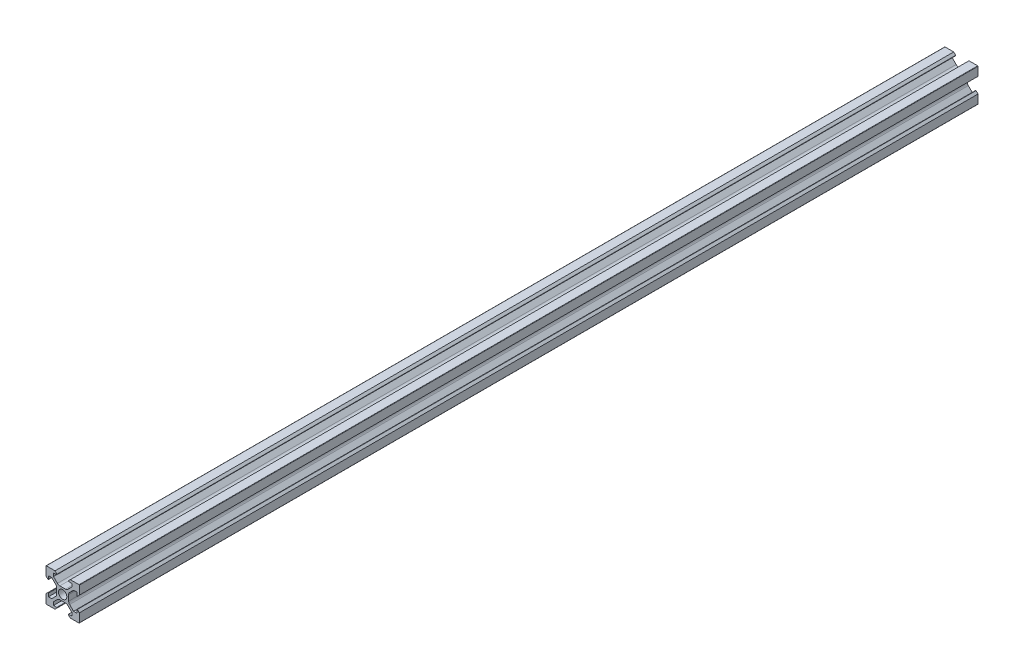
SolidWorks part; units mm, degrees
material "Liga 1350"
ref_plane "Plano frontal" through (0, 0, 0) normal (0, 0, 1) x (1, 0, 0)
ref_plane "Plano superior" through (0, 0, 0) normal (0, 1, 0) x (1, 0, 0)
ref_plane "Plano direito" through (0, 0, 0) normal (1, 0, 0) x (0, 0, -1)
sketch "Esboço1" plane through (0, 0, 0) normal (0, 0, 1) x (1, 0, 0)
  line L0 (0, 13.8681) -> (0, -15.879) construction
  line L1 (-4.6, -10) -> (-9.8, -10)
  line L2 (-3.4414, -8.8414) -> (-4.6, -10)
  line L3 (-4.1858, -3.1251) -> (-6.5607, -5.5)
  line L4 (-10, 9.8) -> (-10, 4.6)
  line L5 (-5.5, -8.5) -> (-3.5828, -8.5)
  line L6 (-5.5, -8.5) -> (-5.5, -6.5607)
  line L7 (-8.5, -5.5) -> (-8.5, -3.5828)
  line L8 (-21.5514, 0) -> (2.5, 0) construction
  line L9 (-3.1251, 4.1858) -> (-5.5, 6.5607)
  line L10 (-8.8414, -3.4414) -> (-10, -4.6)
  line L11 (-8.5, 5.5) -> (-6.5607, 5.5)
  line L12 (-8.8414, 3.4414) -> (-10, 4.6)
  line L13 (-8.5, -5.5) -> (-6.5607, -5.5)
  line L14 (-8.5, 5.5) -> (-8.5, 3.5828)
  line L15 (-3.1251, -4.1858) -> (-5.5, -6.5607)
  line L16 (-21.5514, 0) -> (20.6623, 0) construction
  line L17 (-8.5, 10) -> (-8.5, -10) construction
  line L18 (-10, -9.8) -> (-10, -4.6)
  line L19 (-21.5514, 5.5) -> (20.6623, 5.5) construction
  line L21 (-10, 10) -> (-10, -10) construction
  line L22 (3.6, 1.7109) -> (3.6, 0) construction
  line L23 (21.5514, 0) -> (-2.5, 0) construction
  line L24 (4.6, 10) -> (9.8, 10)
  line L25 (-5.5, 8.5) -> (-5.5, 6.5607)
  line L26 (3.4414, 8.8414) -> (4.6, 10)
  line L27 (-5.5, 8.5) -> (-3.5828, 8.5)
  line L28 (4.1858, 3.1251) -> (6.5607, 5.5)
  line L29 (5.5, 8.5) -> (3.5828, 8.5)
  line L30 (5.5, 8.5) -> (5.5, 6.5607)
  line L31 (-3.6, 1.7109) -> (-3.6, -1.7109)
  line L33 (10, -9.8) -> (10, -4.6)
  line L34 (-4.1858, 3.1251) -> (-6.5607, 5.5)
  line L35 (-3.4414, 8.8414) -> (-4.6, 10)
  line L36 (-4.6, 10) -> (-9.8, 10)
  line L37 (3.1251, -4.1858) -> (5.5, -6.5607)
  line L38 (8.5, 5.5) -> (8.5, 3.5828)
  line L39 (8.5, -5.5) -> (6.5607, -5.5)
  line L40 (8.8414, 3.4414) -> (10, 4.6)
  line L41 (8.5, 5.5) -> (6.5607, 5.5)
  line L42 (8.8414, -3.4414) -> (10, -4.6)
  line L43 (3.1251, 4.1858) -> (5.5, 6.5607)
  line L44 (8.5, -5.5) -> (8.5, -3.5828)
  line L45 (5.5, -8.5) -> (5.5, -6.5607)
  line L46 (5.5, -8.5) -> (3.5828, -8.5)
  line L47 (10, 9.8) -> (10, 4.6)
  line L48 (4.1858, -3.1251) -> (6.5607, -5.5)
  line L49 (3.4414, -8.8414) -> (4.6, -10)
  line L50 (4.6, -10) -> (9.8, -10)
  line L51 (-1.7109, 3.6) -> (1.7109, 3.6)
  line L52 (3.6, 1.7109) -> (3.6, -1.7109)
  line L53 (1.7109, -3.6) -> (-1.7109, -3.6)
  circle A0 centre (0, 0) radius 2.5
  arc A1 (-3.6, 1.7109) -> (-4.1858, 3.1251) centre (-5.6, 1.7109) ccw
  arc A2 (-8.5, 3.5828) -> (-8.8414, 3.4414) centre (-8.7, 3.5828) cw
  arc A3 (-9.8, 10) -> (-10, 9.8) centre (-9.8, 9.8) ccw
  arc A4 (-1.7109, 3.6) -> (-3.1251, 4.1858) centre (-1.7109, 5.6) cw
  arc A5 (-3.5828, 8.5) -> (-3.4414, 8.8414) centre (-3.5828, 8.7) ccw
  arc A6 (-3.5828, -8.5) -> (-3.4414, -8.8414) centre (-3.5828, -8.7) cw
  arc A7 (-1.7109, -3.6) -> (-3.1251, -4.1858) centre (-1.7109, -5.6) ccw
  arc A8 (-9.8, -10) -> (-10, -9.8) centre (-9.8, -9.8) cw
  arc A9 (-8.5, -3.5828) -> (-8.8414, -3.4414) centre (-8.7, -3.5828) ccw
  arc A10 (-3.6, -1.7109) -> (-4.1858, -3.1251) centre (-5.6, -1.7109) cw
  arc A11 (3.6, -1.7109) -> (4.1858, -3.1251) centre (5.6, -1.7109) ccw
  arc A12 (8.5, -3.5828) -> (8.8414, -3.4414) centre (8.7, -3.5828) cw
  arc A13 (9.8, -10) -> (10, -9.8) centre (9.8, -9.8) ccw
  arc A14 (1.7109, -3.6) -> (3.1251, -4.1858) centre (1.7109, -5.6) cw
  arc A15 (3.5828, -8.5) -> (3.4414, -8.8414) centre (3.5828, -8.7) ccw
  arc A16 (3.5828, 8.5) -> (3.4414, 8.8414) centre (3.5828, 8.7) cw
  arc A17 (1.7109, 3.6) -> (3.1251, 4.1858) centre (1.7109, 5.6) ccw
  arc A18 (9.8, 10) -> (10, 9.8) centre (9.8, 9.8) cw
  arc A19 (8.5, 3.5828) -> (8.8414, 3.4414) centre (8.7, 3.5828) ccw
  arc A20 (3.6, 1.7109) -> (4.1858, 3.1251) centre (5.6, 1.7109) cw
  point P0 (0, 0)
  point P45 (-3.6, 2.5393)
extrude "Ressalto-extrusão1" add sketch "Esboço1" along normal blind 540
